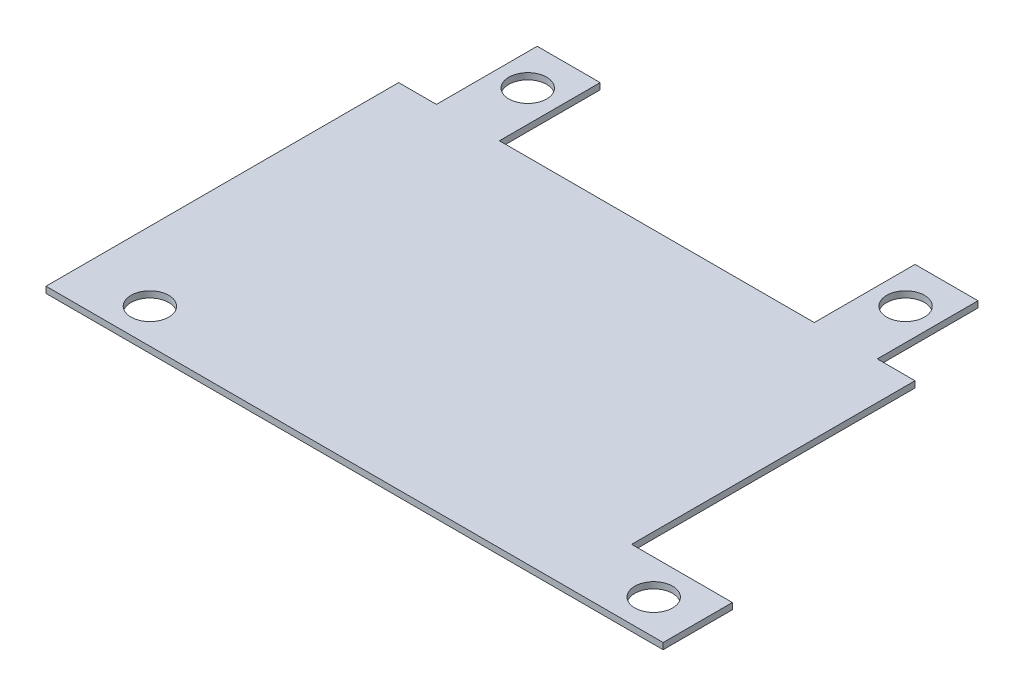
SolidWorks part; units mm, degrees
ref_plane "Front Plane" through (0, 0, 0) normal (0, 0, 1) x (1, 0, 0)
ref_plane "Top Plane" through (0, 0, 0) normal (0, 1, 0) x (1, 0, 0)
ref_plane "Right Plane" through (0, 0, 0) normal (1, 0, 0) x (0, 0, -1)
sketch "Sketch1" plane through (0, 0, 0) normal (0, 1, 0) x (1, 0, 0)
  line L1 (20.5, 14) -> (-20.5, 14)
  line L2 (20.5, 14) -> (20.5, -14)
  line L3 (20.5, -14) -> (-20.5, -14)
  line L4 (-20.5, 14) -> (-20.5, -14)
  line L5 (20.5, 14) -> (-20.5, -14) construction
  line L6 (20.5, -14) -> (-20.5, 14) construction
  point P0 (0, 0)
  dimension "D1" = 28
  dimension "D2" = 41
extrude "Boss-Extrude1" add sketch "Sketch1" along normal blind 0.5
sketch "Sketch2" plane through (0, 0, 0) normal (0, 1, 0) x (1, 0, 0)
  line L0 (20.5, 14) -> (-20.5, 14) construction
  line L1 (-17.5, 14) -> (-12.5, 14)
  line L2 (-17.5, 14) -> (-17.5, 22)
  line L3 (-17.5, 22) -> (-12.5, 22)
  line L4 (-12.5, 14) -> (-12.5, 22)
  line L5 (-15, 14) -> (-15, 50014) construction
  line L6 (12.5, 14) -> (17.5, 14)
  line L7 (12.5, 14) -> (12.5, 22)
  line L8 (12.5, 22) -> (17.5, 22)
  line L9 (17.5, 14) -> (17.5, 22)
  line L10 (20.5, -14) -> (28.5, -14)
  line L11 (20.5, -14) -> (20.5, -8.5)
  line L12 (20.5, -8.5) -> (28.5, -8.5)
  line L13 (28.5, -14) -> (28.5, -8.5)
  line L14 (15, 14) -> (15, 50014) construction
  line L15 (20.5, -11.25) -> (50020.5, -11.25) construction
  line L16 (0, -14) -> (0, 49986) construction
  line L17 (-20.5, -14) -> (20.5, -14) construction
  circle A0 centre (-15, 18.75) radius 1.5
  circle A1 centre (15, 18.75) radius 1.5
  circle A2 centre (-15, -11.25) radius 1.5
  circle A3 centre (25, -11.25) radius 1.5
  point P17 (-15, 14)
  point P18 (-15, 22)
  point P21 (15, 14)
  point P22 (15, 22)
  point P31 (20.5, -11.25)
  point P32 (28.5, -11.25)
  point P39 (0, -14)
  point P40 (0, 14)
  dimension "D7" = 3
  dimension "D1" = 5
  dimension "D2" = 5.5
  dimension "D3" = 5
  dimension "D4" = 30
  dimension "D5" = 8
  dimension "D6" = 30
  dimension "D8" = 40
  dimension "D9" = 8
extrude "Boss-Extrude2" add sketch "Sketch2" along normal up to surface (0.5 mm away) up to face at (0, 0.5, 0)
sketch "Sketch3" plane through (0, 0.5, 0) normal (0, 1, 0) x (1, 0, 0)
  circle A0 centre (-15, -11.25) radius 1.5
  circle A1 centre (-15, -11.25) radius 1.5 construction
extrude "Cut-Extrude1" cut sketch "Sketch3" against normal through all
